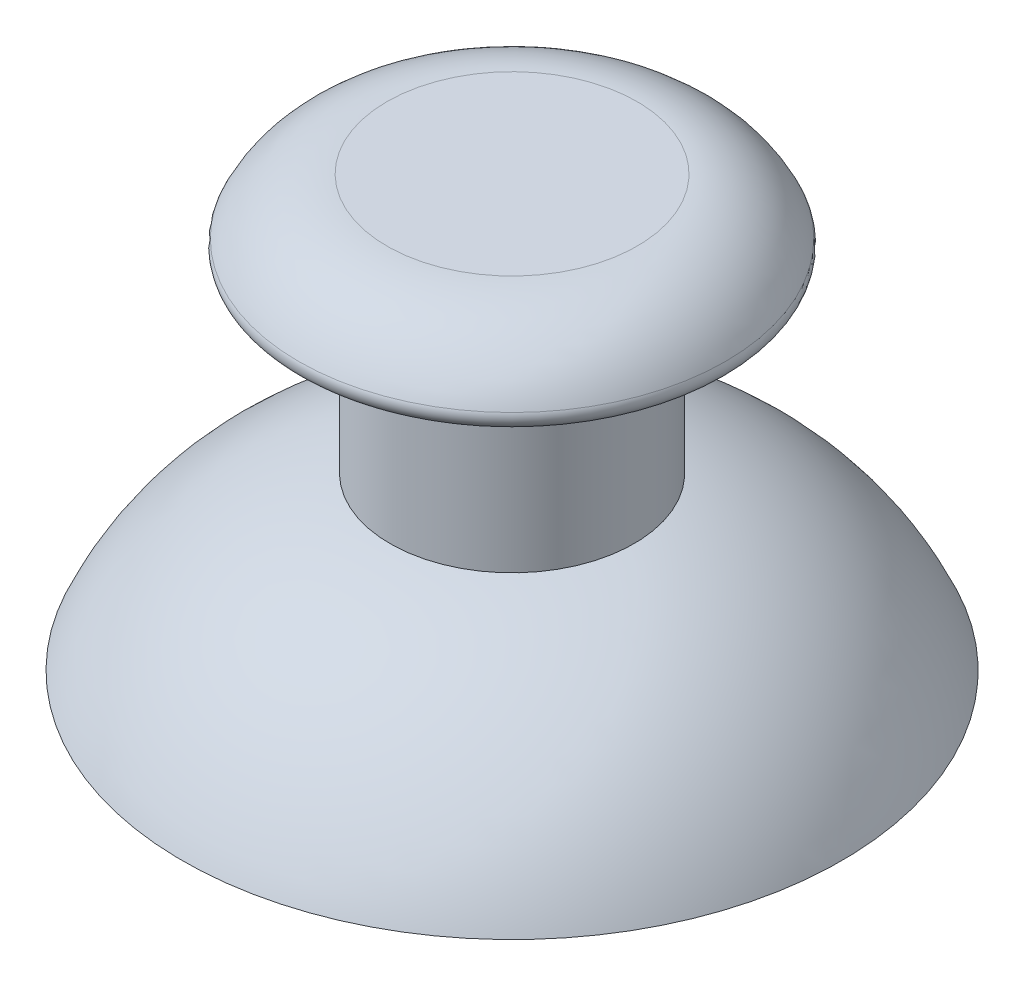
SolidWorks part; units mm, degrees
ref_plane "Front Plane" through (0, 0, 0) normal (0, 0, 1) x (1, 0, 0)
ref_plane "Top Plane" through (0, 0, 0) normal (0, 1, 0) x (1, 0, 0)
ref_plane "Right Plane" through (0, 0, 0) normal (1, 0, 0) x (0, 0, -1)
sketch "Sketch1" plane through (0, 0, 0) normal (0, 0, 1) x (1, 0, 0)
  line L0 (0, 31.6179) -> (0, 20.0224)
  line L1 (-12.4026, 14) -> (-13.5, 14)
  line L2 (-5, 21) -> (-5, 28.6179)
  line L3 (-5, 28.6179) -> (-9, 28.6179)
  line L4 (0, 31.6179) -> (-5.127, 31.6179)
  line L5 (-4.7893, 20.0224) -> (0, 20.0224)
  arc A0 (-13.5, 14) -> (-5, 21) centre (-2.4718, 9.2693) cw
  arc A1 (-9, 28.6179) -> (-5.127, 31.6179) centre (-5.127, 27.6179) cw
  arc A2 (-12.4026, 14) -> (-4.7893, 20.0224) centre (-2.4718, 9.2693) cw
  arc A3 (-12.581, 13.6058) -> (-4.7893, 20.0224) centre (-2.4718, 9.2693) cw construction
  dimension "D5" = 12
  dimension "D1" = 7
  dimension "D2" = 14
  dimension "D3" = 5
  dimension "D4" = 9
  dimension "D7" = 3
  dimension "D9" = 1
revolve "Revolve1" add sketch "Sketch1" angle 360 about L0
fillet "Fillet1" radius 0.5 1 edges at (-9, 28.6179, 0)
